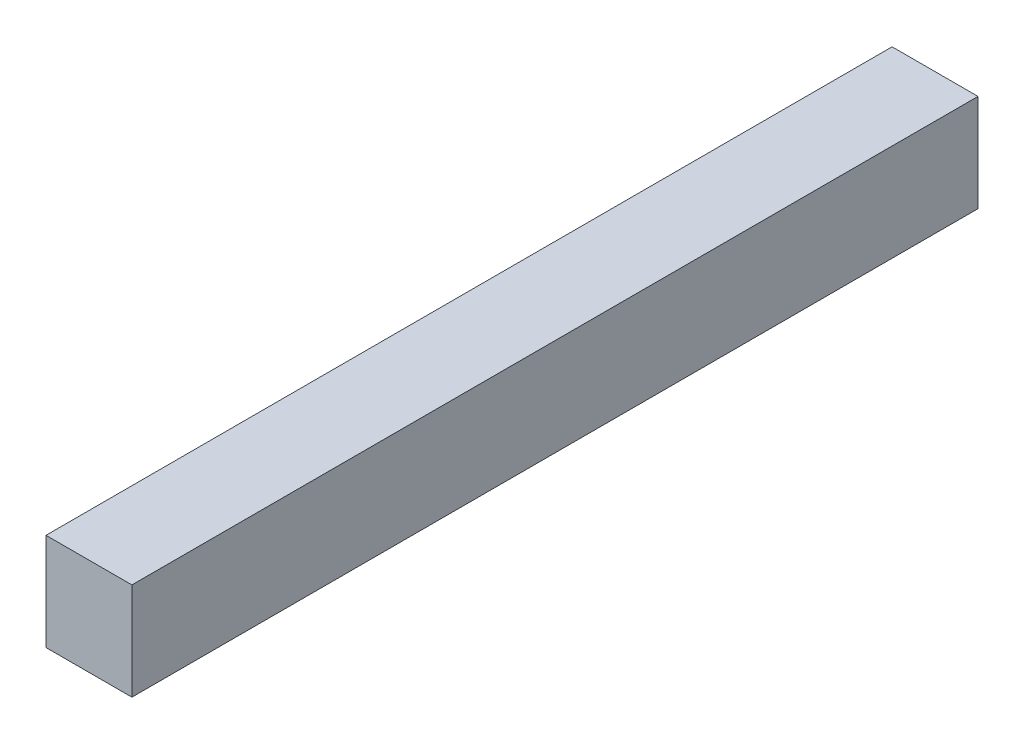
SolidWorks part; units mm, degrees
material "Custom Plastic (5)"
ref_plane "Front Plane" through (0, 0, 0) normal (0, 0, 1) x (1, 0, 0)
ref_plane "Top Plane" through (0, 0, 0) normal (0, 1, 0) x (1, 0, 0)
ref_plane "Right Plane" through (0, 0, 0) normal (1, 0, 0) x (0, 0, -1)
sketch "Battery Pack Cross Section" plane through (0, 0, 0) normal (0, 0, 1) x (1, 0, 0)
  line L1 (-67.31, -76.2) -> (67.31, -76.2)
  line L2 (-67.31, -76.2) -> (-67.31, 76.2)
  line L3 (-67.31, 76.2) -> (67.31, 76.2)
  line L4 (67.31, -76.2) -> (67.31, 76.2)
  line L5 (-67.31, -76.2) -> (67.31, 76.2) construction
  line L6 (-67.31, 76.2) -> (67.31, -76.2) construction
  point P0 (0, 0)
  dimension "D1" = 134.62
  dimension "D2" = 152.4
extrude "Battery Pack" add sketch "Battery Pack Cross Section" along normal mid plane 1325.88
